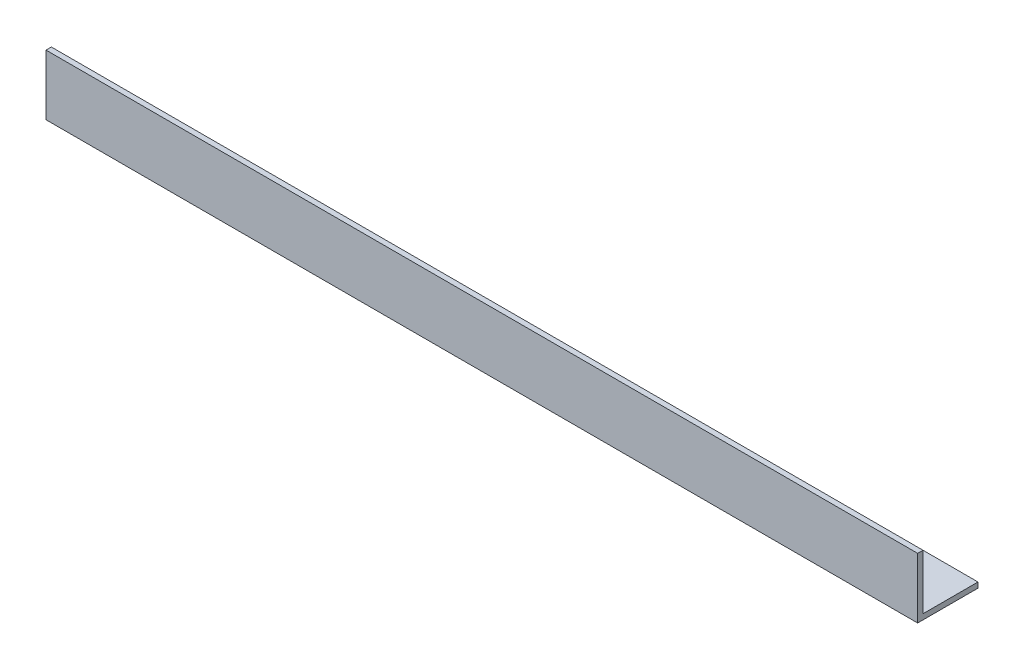
SolidWorks part; units mm, degrees
ref_plane "Спереди" through (0, 0, 0) normal (0, 0, 1) x (1, 0, 0)
ref_plane "Сверху" through (0, 0, 0) normal (0, 1, 0) x (1, 0, 0)
ref_plane "Справа" through (0, 0, 0) normal (1, 0, 0) x (0, 0, -1)
sketch "Эскиз1" plane through (0, 0, 0) normal (1, 0, 0) x (0, 0, -1)
  line L0 (0, 45) -> (0, 0)
  line L1 (0, 0) -> (45, 0)
extrude "Вытянуть-Тонкостенный1" add sketch "Эскиз1" along normal blind 650 thin thin type one direction reverse wall 4
